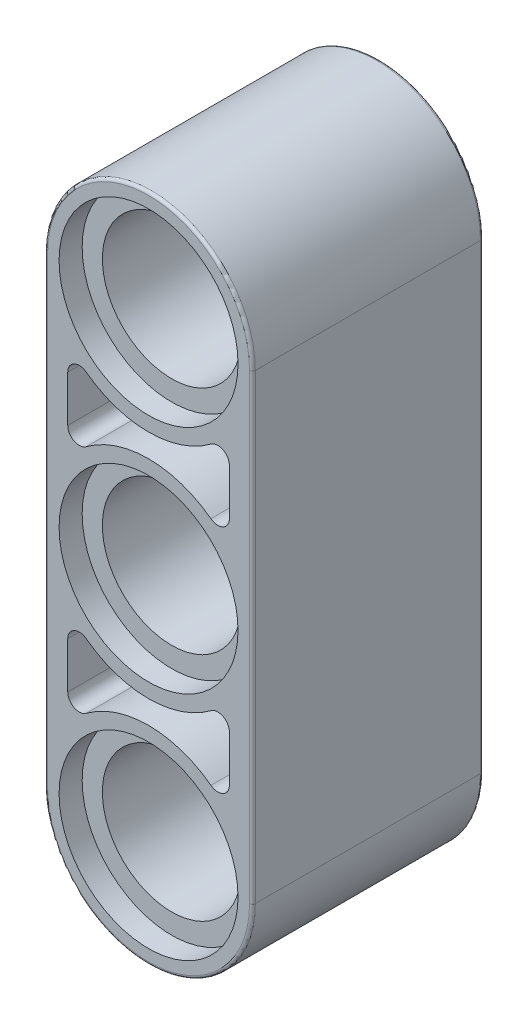
SolidWorks part; units mm, degrees
ref_plane "Front Plane" through (0, 0, 0) normal (0, 0, 1) x (1, 0, 0)
ref_plane "Top Plane" through (0, 0, 0) normal (0, 1, 0) x (1, 0, 0)
ref_plane "Right Plane" through (0, 0, 0) normal (1, 0, 0) x (0, 0, -1)
ref_plane "Plane1" through (0, 0, 4) normal (0, 0, 1) x (1, 0, 0)
sketch "Sketch1" plane through (0, 0, 4) normal (0, 0, 1) x (1, 0, 0)
  line L0 (-3.6, 0) -> (-3.6, -16)
  line L1 (3.6, -16) -> (3.6, 0)
  arc A0 (3.6, 0) -> (-3.6, 0) centre (0, 0) ccw
  arc A1 (-3.6, -16) -> (3.6, -16) centre (0, -16) ccw
  dimension "D1" = 7.2
  dimension "D2" = 16
extrude "Boss-Extrude1" add sketch "Sketch1" against normal blind 8
sketch "Sketch3" plane through (0, 0, 4) normal (0, 0, 1) x (1, 0, 0)
  line L0 (2.8, -4.8) -> (2.8, -3.2)
  line L1 (-2.8, -3.2) -> (-2.8, -4.8)
  arc A0 (2.8, -3.2) -> (2.16, -2.88) centre (2.4, -3.2) ccw
  arc A1 (2.16, -2.88) -> (-2.16, -2.88) centre (0, 0) cw
  arc A2 (-2.16, -2.88) -> (-2.8, -3.2) centre (-2.4, -3.2) ccw
  arc A3 (-2.8, -4.8) -> (-2.16, -5.12) centre (-2.4, -4.8) ccw
  arc A4 (-2.16, -5.12) -> (2.16, -5.12) centre (0, -8) cw
  arc A5 (2.16, -5.12) -> (2.8, -4.8) centre (2.4, -4.8) ccw
extrude "Cut-Extrude2" cut sketch "Sketch3" against normal blind 3.1
sketch "Sketch5" plane through (0, 0, 4) normal (0, 0, 1) x (1, 0, 0)
  line L0 (2.8, -12.8) -> (2.8, -11.2)
  line L1 (-2.8, -11.2) -> (-2.8, -12.8)
  arc A0 (2.8, -11.2) -> (2.16, -10.88) centre (2.4, -11.2) ccw
  arc A1 (2.16, -10.88) -> (-2.16, -10.88) centre (0, -8) cw
  arc A2 (-2.16, -10.88) -> (-2.8, -11.2) centre (-2.4, -11.2) ccw
  arc A3 (-2.8, -12.8) -> (-2.16, -13.12) centre (-2.4, -12.8) ccw
  arc A4 (-2.16, -13.12) -> (2.16, -13.12) centre (0, -16) cw
  arc A5 (2.16, -13.12) -> (2.8, -12.8) centre (2.4, -12.8) ccw
extrude "Cut-Extrude4" cut sketch "Sketch5" against normal blind 3.1
sketch "Sketch7" plane through (0, 0, -4) normal (0, 0, -1) x (-1, 0, 0)
  line L0 (2.8, -4.8) -> (2.8, -3.2)
  line L1 (-2.8, -3.2) -> (-2.8, -4.8)
  arc A0 (2.8, -3.2) -> (2.16, -2.88) centre (2.4, -3.2) ccw
  arc A1 (2.16, -2.88) -> (-2.16, -2.88) centre (0, 0) cw
  arc A2 (-2.16, -2.88) -> (-2.8, -3.2) centre (-2.4, -3.2) ccw
  arc A3 (-2.8, -4.8) -> (-2.16, -5.12) centre (-2.4, -4.8) ccw
  arc A4 (-2.16, -5.12) -> (2.16, -5.12) centre (0, -8) cw
  arc A5 (2.16, -5.12) -> (2.8, -4.8) centre (2.4, -4.8) ccw
extrude "Cut-Extrude6" cut sketch "Sketch7" against normal blind 3.1
sketch "Sketch8" plane through (0, 0, -4) normal (0, 0, -1) x (-1, 0, 0)
  line L0 (-2.8, -11.2) -> (-2.8, -12.8)
  line L1 (2.8, -12.8) -> (2.8, -11.2)
  arc A0 (2.16, -10.88) -> (-2.16, -10.88) centre (0, -8) cw
  arc A1 (-2.16, -10.88) -> (-2.8, -11.2) centre (-2.4, -11.2) ccw
  arc A2 (-2.8, -12.8) -> (-2.16, -13.12) centre (-2.4, -12.8) ccw
  arc A3 (-2.16, -13.12) -> (2.16, -13.12) centre (0, -16) cw
  arc A4 (2.16, -13.12) -> (2.8, -12.8) centre (2.4, -12.8) ccw
  arc A5 (2.8, -11.2) -> (2.16, -10.88) centre (2.4, -11.2) ccw
extrude "Cut-Extrude7" cut sketch "Sketch8" against normal blind 3.1
ref_plane "Plane2" through (0, -16, 0) normal (0, 1, 0) x (1, 0, 0)
sketch "Sketch10" plane through (0, -16, 0) normal (0, 1, 0) x (1, 0, 0)
  line L0 (3.1, 4) -> (0, 4)
  line L1 (0, 4) -> (0, -4)
  line L2 (0, -4) -> (3.1, -4)
  line L3 (3.1, -4) -> (3.1, -3.2)
  line L4 (3.1, -3.2) -> (2.4, -3.2)
  line L5 (2.4, -3.2) -> (2.4, 3.2)
  line L6 (2.4, 3.2) -> (3.1, 3.2)
  line L7 (3.1, 3.2) -> (3.1, 4)
  line L8 (0, 4) -> (0, -4) construction
revolve "Cut-Revolve1" cut sketch "Sketch10" angle 360 about L8
ref_plane "Plane3" through (0, 16, 0) normal (0, 1, 0) x (1, 0, 0)
ref_plane "Plane4" through (0, -8, 0) normal (0, 1, 0) x (1, 0, 0)
sketch "Sketch12" plane through (0, -8, 0) normal (0, 1, 0) x (1, 0, 0)
  line L0 (3.1, 4) -> (0, 4)
  line L1 (0, 4) -> (0, -4)
  line L2 (0, -4) -> (3.1, -4)
  line L3 (3.1, -4) -> (3.1, -3.2)
  line L4 (3.1, -3.2) -> (2.4, -3.2)
  line L5 (2.4, -3.2) -> (2.4, 3.2)
  line L6 (2.4, 3.2) -> (3.1, 3.2)
  line L7 (3.1, 3.2) -> (3.1, 4)
  line L8 (0, 4) -> (0, -4) construction
revolve "Cut-Revolve3" cut sketch "Sketch12" angle 360 about L8
sketch "Sketch13" plane through (0, 0, 0) normal (0, 1, 0) x (1, 0, 0)
  line L0 (3.1, 4) -> (0, 4)
  line L1 (0, 4) -> (0, -4)
  line L2 (0, -4) -> (3.1, -4)
  line L3 (3.1, -4) -> (3.1, -3.2)
  line L4 (3.1, -3.2) -> (2.4, -3.2)
  line L5 (2.4, -3.2) -> (2.4, 3.2)
  line L6 (2.4, 3.2) -> (3.1, 3.2)
  line L7 (3.1, 3.2) -> (3.1, 4)
  line L8 (0, 4) -> (0, -4) construction
revolve "Cut-Revolve4" cut sketch "Sketch13" angle 360 about L8
ref_plane "Plane5" through (0, 8, 0) normal (0, 1, 0) x (1, 0, 0)
fillet "Fillet1" radius 0.1 8 edges at (0, -19.6, -4) (-3.6, -8, -4) (3.6, -8, -4) (0, 3.6, -4) (0, -19.6, 4) (-3.6, -8, 4) (3.6, -8, 4) (0, 3.6, 4)
